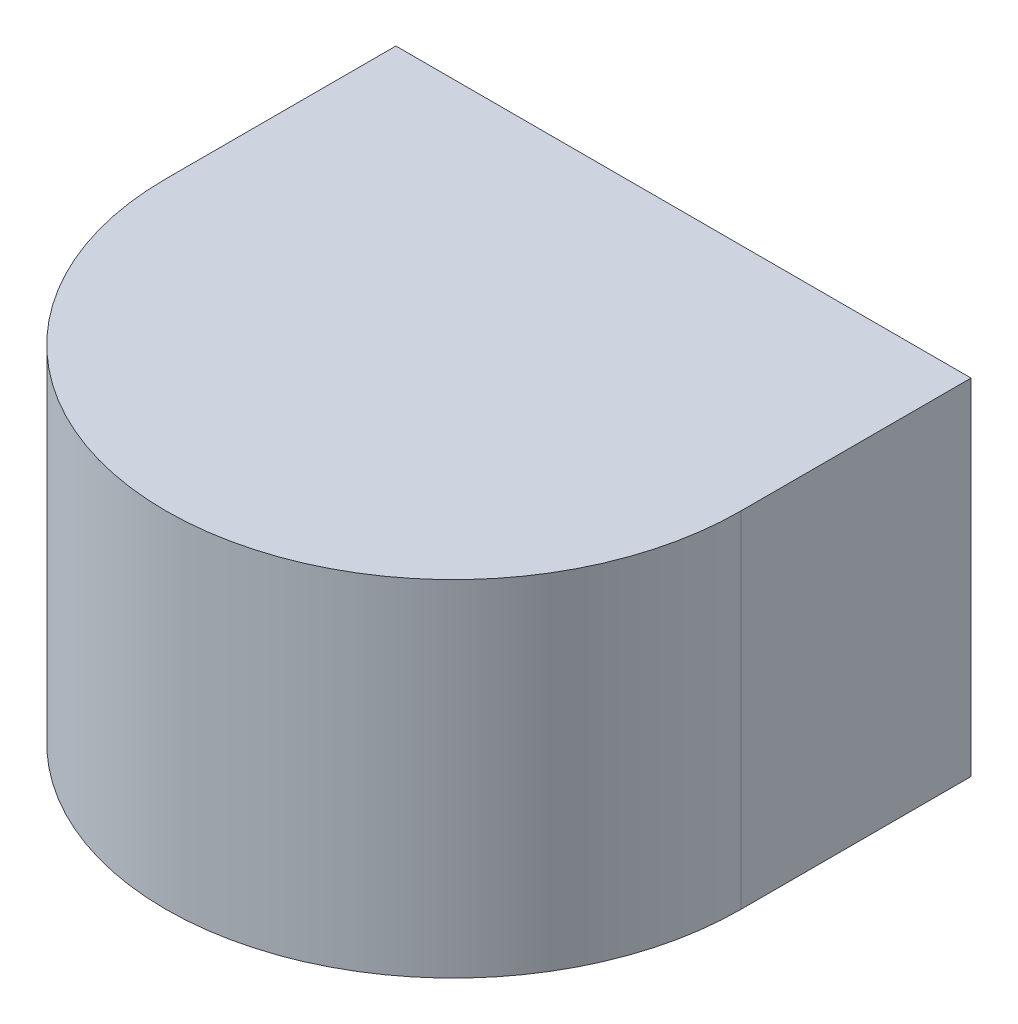
SolidWorks part; units mm, degrees
ref_plane "Front Plane" through (0, 0, 0) normal (0, 0, 1) x (1, 0, 0)
ref_plane "Top Plane" through (0, 0, 0) normal (0, 1, 0) x (1, 0, 0)
ref_plane "Right Plane" through (0, 0, 0) normal (1, 0, 0) x (0, 0, -1)
sketch "Sketch3" plane through (0, 0, 0) normal (0, 1, 0) x (1, 0, 0)
  line L0 (-125, 0) -> (125, 0) construction
  line L1 (0, 0) -> (0, 70) construction
  line L2 (-125, 0) -> (-125, 100)
  line L3 (-125, 100) -> (-100, 100)
  line L4 (-100, 100) -> (-100, 70)
  line L5 (-100, 70) -> (100, 70)
  line L6 (100, 100) -> (100, 70)
  line L7 (125, 100) -> (100, 100)
  line L8 (125, 0) -> (125, 100)
  arc A0 (125, 0) -> (-125, 0) centre (0, 0) cw
  point P3 (0, 0)
  point P14 (0, 70)
  dimension "D1" = 250
  dimension "D2" = 100
  dimension "D3" = 30
  dimension "D4" = 200
extrude "Boss-Extrude1" add sketch "Sketch3" along normal blind 100
sketch "Sketch4" plane through (0, 100, 0) normal (0, 1, 0) x (1, 0, 0)
  line L0 (-100, 100) -> (100, 100)
  line L7 (125, 0) -> (125, 100)
  line L8 (125, 100) -> (100, 100)
  line L9 (100, 100) -> (100, 70)
  line L10 (100, 70) -> (-100, 70)
  line L11 (-100, 70) -> (-100, 100)
  line L12 (-100, 100) -> (-125, 100)
  line L13 (-125, 100) -> (-125, 0)
  line L14 (125, 0) -> (125, 100)
  line L15 (125, 100) -> (100, 100)
  line L19 (-100, 100) -> (-125, 100)
  line L20 (-125, 100) -> (-125, 0)
  arc A1 (-125, 0) -> (125, 0) centre (0, 0) ccw
  arc A2 (-125, 0) -> (125, 0) centre (0, 0) ccw
  dimension "D1" = 0
extrude "Boss-Extrude2" add sketch "Sketch4" along normal blind 50
sketch "Sketch5" plane through (0, 0, 0) normal (0, -1, 0) x (1, 0, 0)
  line L0 (0, 134.3471) -> (0, -106.0391) construction
  line L1 (-125, 0) -> (125, 0) construction
  line L2 (-113, -22.5) -> (-83, -22.5)
  line L3 (-113, -22.5) -> (-113, 22.5)
  line L4 (-113, 22.5) -> (-83, 22.5)
  line L5 (-83, -22.5) -> (-83, 22.5)
  line L6 (-113, -22.5) -> (-83, 22.5) construction
  line L7 (-113, 22.5) -> (-83, -22.5) construction
  line L8 (125, 0) -> (125, -100) construction
  line L9 (-125, -100) -> (-125, 0) construction
  line L10 (113, 22.5) -> (83, -22.5) construction
  line L11 (113, -22.5) -> (83, 22.5) construction
  line L12 (83, -22.5) -> (83, 22.5)
  line L13 (113, 22.5) -> (83, 22.5)
  line L14 (113, -22.5) -> (113, 22.5)
  line L15 (113, -22.5) -> (83, -22.5)
  point P4 (-98, 0)
  point P21 (98, 0)
  dimension "D1" = 12
  dimension "D2" = 30
  dimension "D3" = 45
extrude "Cut-Extrude1" cut sketch "Sketch5" against normal blind 20
